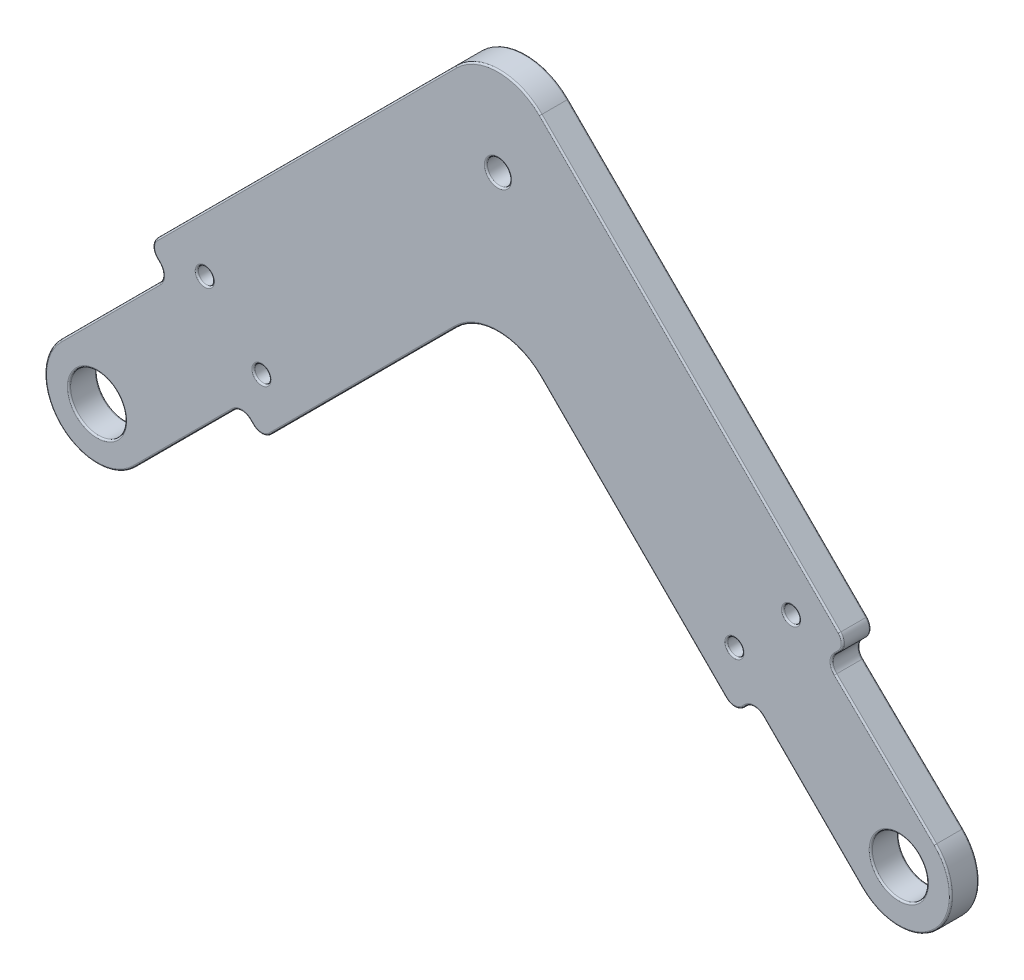
SolidWorks part; units mm, degrees
ref_plane "Front Plane" through (0, 0, 0) normal (0, 0, 1) x (1, 0, 0)
ref_plane "Top Plane" through (0, 0, 0) normal (0, 1, 0) x (1, 0, 0)
ref_plane "Right Plane" through (0, 0, 0) normal (1, 0, 0) x (0, 0, -1)
sketch "Sketch1" plane through (0, 0, 0) normal (0, 0, 1) x (1, 0, 0)
  line L0 (-100, 0) -> (100, 0) construction
  line L1 (-100, 0) -> (0, 100) construction
  line L2 (0, 100) -> (100, 0) construction
  line L3 (0, 100) -> (0, 60) construction
  line L4 (-40, 60) -> (40, 60) construction
  line L5 (0, 0) -> (-50, 50) construction
  circle A0 centre (-100, 0) radius 20
  circle A1 centre (0, 0) radius 20
  circle A2 centre (100, 0) radius 20
  point P4 (0, 0)
  point P9 (0, 60)
  dimension "D1" = 40
  dimension "D2" = 200
  dimension "D3" = 90
  dimension "D4" = 80
  dimension "D5" = 90
sketch "Sketch2" plane through (0, 0, 0) normal (0, 0, 1) x (1, 0, 0)
  line L0 (-56.5165, 43.4835) -> (-40, 60) construction
  line L1 (-100, 0) -> (0, 100) construction
  line L2 (-40, 60) -> (40, 60) construction
  line L3 (40, 60) -> (86.565, 13.435) construction
  line L4 (0, 100) -> (100, 0) construction
  line L5 (-49.4454, 36.4124) -> (-35.8579, 50)
  line L6 (-35.8579, 50) -> (35.8579, 50)
  line L7 (35.8579, 50) -> (79.4939, 6.364)
  line L8 (-63.5876, 50.5546) -> (-44.1421, 70)
  line L9 (-44.1421, 70) -> (44.1421, 70)
  line L10 (44.1421, 70) -> (93.636, 20.5061)
  line L11 (-63.5876, 50.5546) -> (-49.4454, 36.4124)
  line L12 (79.4939, 6.364) -> (93.636, 20.5061)
  line L13 (104.5962, 4.5962) -> (91.1612, 18.0312)
  line L14 (81.9688, 8.8388) -> (95.4038, -4.5962)
  line L15 (75.9584, 9.8995) -> (90.1005, 24.0416) construction
  line L16 (0, 100) -> (0, 60) construction
  line L17 (-3.4532, 85.4203) -> (-6, 70)
  line L18 (0, 84.85) -> (0, 84.8364) construction
  line L19 (3.4532, 85.4203) -> (6, 70)
  circle A0 centre (100, 0) radius 3.5
  circle A1 centre (100, 0) radius 10 construction
  arc A2 (95.4038, -4.5962) -> (104.5962, 4.5962) centre (100, 0) ccw
  circle A3 centre (79.4939, 13.435) radius 1
  circle A4 centre (100, 0) radius 6.5 construction
  circle A5 centre (86.565, 20.5061) radius 1
  circle A6 centre (0, 84.85) radius 1.5
  arc A7 (3.4532, 85.4203) -> (-3.4532, 85.4203) centre (0, 84.85) ccw
  circle A8 centre (0, 60) radius 1.5
  circle A9 centre (-50, 50) radius 1.5
  circle A10 centre (0, 84.85) radius 3.5 construction
  point P28 (106.5, 0)
  point P48 (3.5, 82)
  dimension "D4" = 7
  dimension "D5" = 20
  dimension "D9" = 2
  dimension "D11" = 14.85
  dimension "D12" = 3
  dimension "D14" = 6
  dimension "D15" = 3
  dimension "D1" = 10
  dimension "D3" = 27.5
  dimension "D7" = 19
  dimension "D8" = 5
  dimension "D10" = 5
  dimension "D2" = 10
  dimension "D6" = 3
  dimension "D13" = 2
sketch "Sketch3" plane through (0, 0, 0) normal (0, 0, 1) x (1, 0, 0)
  line L0 (-86.565, 13.435) -> (-50, 50) construction
  line L1 (-100, 0) -> (0, 100) construction
  line L2 (-50, 50) -> (-13.435, 13.435) construction
  line L3 (0, 0) -> (-50, 50) construction
  line L4 (-79.4939, 6.364) -> (-50, 35.8579)
  line L5 (-50, 35.8579) -> (-20.5061, 6.364)
  line L6 (-93.636, 20.5061) -> (-50, 64.1421)
  line L7 (-50, 64.1421) -> (-6.364, 20.5061)
  line L8 (-93.636, 20.5061) -> (-79.4939, 6.364)
  line L9 (-20.5061, 6.364) -> (-6.364, 20.5061)
  line L10 (-104.5962, 4.5962) -> (-91.1612, 18.0312)
  line L11 (-95.4038, -4.5962) -> (-81.9688, 8.8388)
  line L12 (-4.5962, -4.5962) -> (-18.0312, 8.8388)
  line L13 (4.534, 4.6576) -> (-9.0191, 17.8509)
  line L14 (-90.1005, 24.0416) -> (-75.9584, 9.8995) construction
  line L15 (-24.0416, 9.8995) -> (-9.8995, 24.0416) construction
  circle A0 centre (-100, 0) radius 3.5
  circle A1 centre (-100, 0) radius 10 construction
  circle A2 centre (0, 0) radius 3.5
  circle A3 centre (0, 0) radius 10 construction
  arc A4 (-4.5962, -4.5962) -> (4.534, 4.6576) centre (0, 0) ccw
  arc A5 (-104.5962, 4.5962) -> (-95.4038, -4.5962) centre (-100, 0) ccw
  circle A7 centre (0, 0) radius 20 construction
  circle A8 centre (-86.565, 20.5061) radius 1
  circle A9 centre (0, 0) radius 6.5 construction
  circle A10 centre (-79.4939, 13.435) radius 1
  circle A11 centre (-20.5061, 13.435) radius 1
  circle A12 centre (-13.435, 20.5061) radius 1
  circle A13 centre (-50, 50) radius 1.5 construction
  circle A14 centre (-50, 50) radius 1.5
  point P34 (6.5, 0)
  dimension "D1" = 7
  dimension "D2" = 20
  dimension "D4" = 10
  dimension "D10" = 2
  dimension "D6" = 19
  dimension "D7" = 19
  dimension "D8" = 5
  dimension "D9" = 5
  dimension "D11" = 5
  dimension "D12" = 5
  dimension "D3" = 3
  dimension "D5" = 10
sketch "Sketch4" plane through (0, 0, 0) normal (0, 0, 1) x (1, 0, 0)
  line L0 (0, 60) -> (0, 138.097) construction
  line L1 (-57.5, 93.3579) -> (57.5, 93.3579)
  line L2 (57.5, 93.3579) -> (57.5, 83.3579)
  line L3 (57.5, 83.3579) -> (44.1421, 70)
  line L4 (-44.1421, 70) -> (44.1421, 70) construction
  line L5 (44.1421, 70) -> (-44.1421, 70)
  line L6 (44.1421, 70) -> (93.636, 20.5061) construction
  line L7 (4, 60) -> (4, 70)
  line L8 (-4, 60) -> (-4, 70)
  line L9 (-57.5, 83.3579) -> (-44.1421, 70)
  line L10 (-57.5, 93.3579) -> (-57.5, 83.3579)
  line L11 (-22.5, 84.8579) -> (22.5, 84.8579) construction
  line L12 (-22.5, 89.3579) -> (22.5, 89.3579)
  line L13 (-22.5, 80.3579) -> (22.5, 80.3579)
  circle A0 centre (0, 60) radius 1.5 construction
  circle A1 centre (0, 60) radius 1.5
  arc A2 (-4, 60) -> (4, 60) centre (0, 60) ccw
  arc A3 (-22.5, 89.3579) -> (-22.5, 80.3579) centre (-22.5, 84.8579) ccw
  circle A4 centre (0, 60) radius 4 construction
  arc A5 (22.5, 80.3579) -> (22.5, 89.3579) centre (22.5, 84.8579) ccw
  point P23 (4, 60)
  point P25 (0, 70)
  point P27 (0, 93.3579)
  point P29 (0, 84.8579)
  dimension "D1" = 57.5
  dimension "D2" = 10
  dimension "D4" = 45
  dimension "D5" = 9
  dimension "D6" = 4
  dimension "D3" = 2.5
sketch "Sketch5" plane through (0, 0, 0) normal (0, 0, 1) x (1, 0, 0)
  line L0 (4.534, 4.6576) -> (-9.0191, 17.8509) construction
  line L1 (-4.5962, -4.5962) -> (-18.0312, 8.8388) construction
  line L2 (-104.5962, 4.5962) -> (-91.1612, 18.0312) construction
  line L3 (-95.4038, -4.5962) -> (-81.9688, 8.8388) construction
  line L4 (4.534, 4.6576) -> (-9.0191, 17.8509)
  line L5 (-4.5962, -4.5962) -> (-18.0312, 8.8388)
  line L6 (-79.4939, 6.364) -> (-50, 35.8579)
  line L7 (-50, 35.8579) -> (-20.5061, 6.364)
  line L8 (-20.5061, 6.364) -> (-6.364, 20.5061)
  line L9 (-6.364, 20.5061) -> (-50, 64.1421)
  line L10 (-50, 64.1421) -> (-93.636, 20.5061)
  line L11 (-93.636, 20.5061) -> (-79.4939, 6.364)
  line L12 (-79.4939, 6.364) -> (-50, 35.8579)
  line L13 (-50, 35.8579) -> (-20.5061, 6.364)
  line L14 (-20.5061, 6.364) -> (-18.0312, 8.8388)
  line L15 (-6.364, 20.5061) -> (-50, 64.1421)
  line L16 (-50, 64.1421) -> (-93.636, 20.5061)
  line L17 (-93.636, 20.5061) -> (-91.1612, 18.0312)
  line L18 (-104.5962, 4.5962) -> (-91.1612, 18.0312)
  line L19 (-95.4038, -4.5962) -> (-81.9688, 8.8388)
  line L20 (-81.9688, 8.8388) -> (-79.4939, 6.364)
  line L21 (-9.0191, 17.8509) -> (-6.364, 20.5061)
  arc A0 (-4.5962, -4.5962) -> (4.534, 4.6576) centre (0, 0) ccw construction
  circle A1 centre (0, 0) radius 3.5
  circle A2 centre (0, 0) radius 3.5
  circle A3 centre (-100, 0) radius 3.5
  circle A4 centre (-100, 0) radius 3.5
  circle A5 centre (-13.435, 20.5061) radius 1
  circle A6 centre (-13.435, 20.5061) radius 1
  circle A7 centre (-20.5061, 13.435) radius 1
  circle A8 centre (-20.5061, 13.435) radius 1
  circle A9 centre (-79.4939, 13.435) radius 1
  circle A10 centre (-79.4939, 13.435) radius 1
  circle A11 centre (-86.565, 20.5061) radius 1
  circle A12 centre (-86.565, 20.5061) radius 1
  circle A13 centre (-50, 50) radius 1.5
  circle A14 centre (-50, 50) radius 1.5
  arc A15 (-104.5962, 4.5962) -> (-95.4038, -4.5962) centre (-100, 0) ccw construction
  arc A16 (-4.5962, -4.5962) -> (4.534, 4.6576) centre (0, 0) ccw
  arc A17 (-104.5962, 4.5962) -> (-95.4038, -4.5962) centre (-100, 0) ccw
  dimension "D1" = 0
  dimension "D2" = 0
  dimension "D3" = 0
  dimension "D4" = 0
  dimension "D5" = 0
  dimension "D6" = 0
  dimension "D7" = 0
  dimension "D8" = 0
extrude "Boss-Extrude1" add sketch "Sketch5" against normal blind 3.5
fillet "Fillet1" radius 7.5 2 edges at (-50, 64.1421, -1.75) (-50, 35.8579, -1.75)
fillet "Fillet2" radius 1.5 8 edges at (-93.636, 20.5061, -1.75) (-91.1612, 18.0312, -1.75) (-79.4939, 6.364, -1.75) (-81.9688, 8.8388, -1.75) (-20.5061, 6.364, -1.75) (-18.0312, 8.8388, -1.75) (-6.364, 20.5061, -1.75) (-9.0191, 17.8509, -1.75)
fillet "Fillet3" radius 0.2 62 edges at (-91.7825, 18.0312, -3.5) (-98.409, 10.7834, -3.5) (-104.5962, -4.5962, -3.5) (-89.2166, 1.591, -3.5) (-81.9688, 8.2175, -3.5) (-80.7313, 7.6014, -3.5) (-79.4939, 6.9853, -3.5) (-66.8683, 18.9896, -3.5) (-50, 32.7513, -3.5) (-33.1317, 18.9896, -3.5) (-20.5061, 6.9853, -3.5) (-19.2687, 7.6014, -3.5) (-18.0312, 8.2175, -3.5) (-10.7834, 1.591, -3.5) (4.627, -4.5652, -3.5) (-1.6979, 10.724, -3.5) (-8.3834, 17.8552, -3.5) (-7.6844, 19.1857, -3.5) (-6.9853, 20.5061, -3.5) (-26.0607, 40.2028, -3.5) (-50, 61.0355, -3.5) (-73.9393, 40.2028, -3.5) (-93.0147, 20.5061, -3.5) (-92.3986, 19.2687, -3.5) (3.5, 0, -3.5) (-96.5, 0, -3.5) (-12.435, 20.5061, -3.5) (-19.5061, 13.435, -3.5) (-78.4939, 13.435, -3.5) (-85.565, 20.5061, -3.5) (-48.5, 50, -3.5) (-50, 61.0355, 0) (-26.0607, 40.2028, 0) (-6.9853, 20.5061, 0) (-7.6844, 19.1857, 0) (-8.3834, 17.8552, 0) (-1.6979, 10.724, 0) (4.627, -4.5652, 0) (-10.7834, 1.591, 0) (-18.0312, 8.2175, 0) (-19.2687, 7.6014, 0) (-20.5061, 6.9853, 0) (-33.1317, 18.9896, 0) (-50, 32.7513, 0) (-66.8683, 18.9896, 0) (-79.4939, 6.9853, 0) (-80.7313, 7.6014, 0) (-81.9688, 8.2175, 0) (-89.2166, 1.591, 0) (-104.5962, -4.5962, 0) (-98.409, 10.7834, 0) (-91.7825, 18.0312, 0) (-92.3986, 19.2687, 0) (-93.0147, 20.5061, 0) (-73.9393, 40.2028, 0) (3.5, 0, 0) (-96.5, 0, 0) (-12.435, 20.5061, 0) (-19.5061, 13.435, 0) (-78.4939, 13.435, 0) (-85.565, 20.5061, 0) (-48.5, 50, 0)
